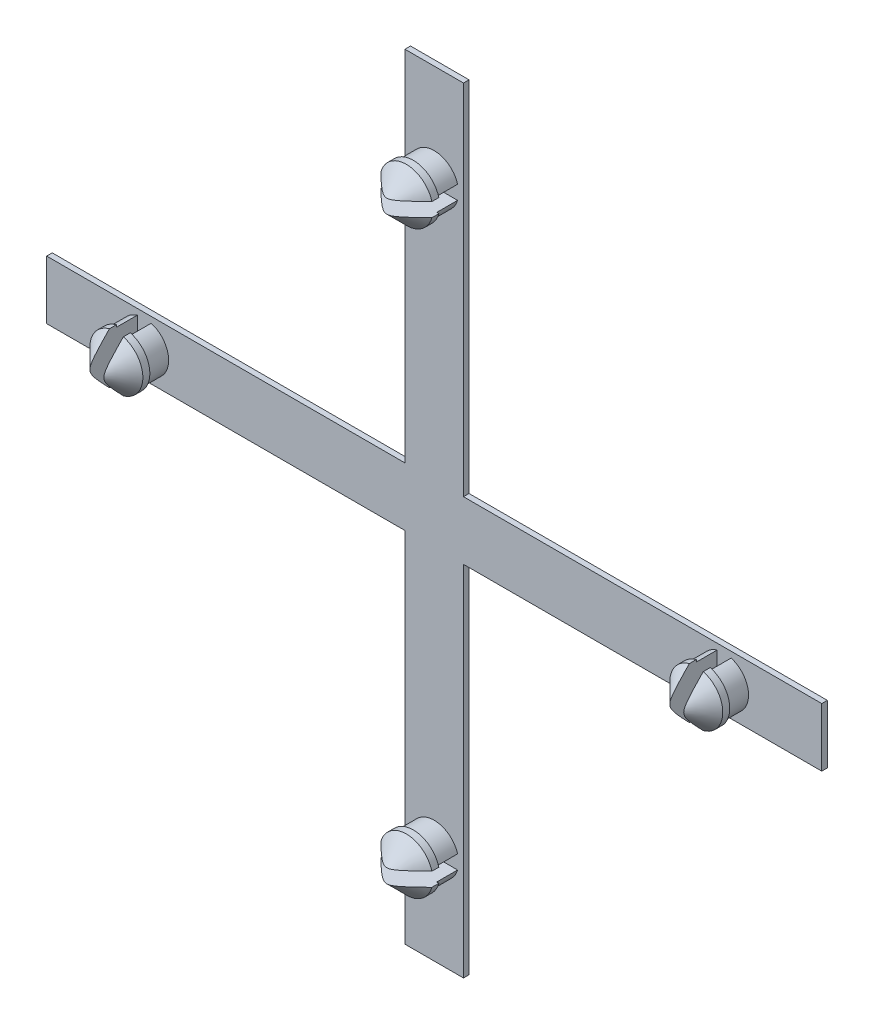
SolidWorks part; units mm, degrees
ref_plane "Přední rovina" through (0, 0, 0) normal (0, 0, 1) x (1, 0, 0)
ref_plane "Horní rovina" through (0, 0, 0) normal (0, 1, 0) x (1, 0, 0)
ref_plane "Pravá rovina" through (0, 0, 0) normal (1, 0, 0) x (0, 0, -1)
sketch "Skica2" plane through (0, 0, 0) normal (0, 0, 1) x (1, 0, 0)
  line L0 (2.1, 27.8) -> (2.1, -27.8)
  line L1 (-27.8, 2.1) -> (27.8, 2.1)
  line L2 (-27.8, 2.1) -> (-27.8, -2.1)
  line L3 (-27.8, -2.1) -> (27.8, -2.1)
  line L4 (27.8, 2.1) -> (27.8, -2.1)
  line L5 (-27.8, 2.1) -> (27.8, -2.1) construction
  line L6 (-27.8, -2.1) -> (27.8, 2.1) construction
  line L7 (2.1, 27.8) -> (-2.1, 27.8)
  line L8 (2.1, -27.8) -> (-2.1, -27.8)
  line L9 (-2.1, 27.8) -> (-2.1, -27.8)
  line L10 (27.8, -2.1) -> (-27.8, -2.1)
  line L11 (27.8, -2.1) -> (27.8, 2.1)
  line L12 (-27.8, -2.1) -> (-27.8, 2.1)
  line L13 (27.8, 2.1) -> (-27.8, 2.1)
  line L14 (-2.1, -27.8) -> (-2.1, 27.8)
  line L15 (-2.1, -27.8) -> (2.1, -27.8)
  line L16 (-2.1, 27.8) -> (2.1, 27.8)
  line L17 (2.1, -27.8) -> (2.1, 27.8)
  point P0 (0, 0)
  point P5 (0, 0)
  point P22 (0, 0)
  dimension "D1" = 4.2
  dimension "D2" = 55.6
  dimension "D3" = 4
  dimension "D7" = 0
extrude "Přidat vysunutím2" add sketch "Skica2" along normal blind 0.4 contours L9 L1 L2 L3 | L4 L1 L0 L3
sketch "Skica3" plane through (0, 0, 0.4) normal (0, 0, 1) x (1, 0, 0)
  line L0 (-27.8, 2.1) -> (-27.8, -2.1) construction
  line L1 (27.8, -2.1) -> (27.8, 2.1) construction
  line L2 (27.8, 2.1) -> (-27.8, 2.1) construction
  line L3 (-27.8, -2.1) -> (27.8, -2.1) construction
  circle A0 centre (-20.8, 0) radius 1.75
  circle A1 centre (20.8, 0) radius 1.75
  circle A2 centre (0, 20.8) radius 1.75
  circle A3 centre (0, -20.8) radius 1.75
  circle A4 centre (20.8, 0) radius 1.75
  circle A5 centre (-20.8, 0) radius 1.75
  circle A6 centre (0, -20.8) radius 1.75
  circle A7 centre (0, 20.8) radius 1.75
  point P27 (0, 0)
  dimension "D1" = 3.5
  dimension "D3" = 3.5
  dimension "D2" = 7
  dimension "D4" = 7
  dimension "D5" = 2.1
  dimension "D6" = 2.1
  dimension "D7" = 4
extrude "Přidat vysunutím3" add sketch "Skica3" along normal blind 1.5 contours A0 | A2 | A1 | A3
sketch "Skica5" plane through (0, 0, 1.9) normal (0, 0, 1) x (1, 0, 0)
  circle A0 centre (-20.8, 0) radius 1.9
  circle A1 centre (20.8, 0) radius 1.9
  circle A2 centre (0, 20.8) radius 1.9
  circle A3 centre (0, -20.8) radius 1.9
  circle A4 centre (20.8, 0) radius 1.9
  circle A5 centre (-20.8, 0) radius 1.9
  circle A6 centre (0, -20.8) radius 1.9
  circle A7 centre (0, 20.8) radius 1.9
  point P21 (0, 0)
  dimension "D1" = 3.8
  dimension "D2" = 3.8
  dimension "D3" = 4
extrude "Přidat vysunutím5" add sketch "Skica5" along normal blind 2 contours A2 | A0 | A1 | A3
chamfer "Zkosení2" distance 1.5 angle 45 4 edges at (1.9, -20.8, 3.9) (22.7, 0, 3.9) (1.9, 20.8, 3.9) (-18.9, 0, 3.9)
sketch "Skica7" plane through (0, 0, 3.9) normal (0, 0, 1) x (1, 0, 0)
  line L0 (2.5, 20.3) -> (-2.5, 20.3)
  line L1 (-20.3, 2.5) -> (-21.3, 2.5)
  line L2 (-20.3, 2.5) -> (-20.3, -2.5)
  line L3 (-20.3, -2.5) -> (-21.3, -2.5)
  line L4 (-21.3, 2.5) -> (-21.3, -2.5)
  line L5 (-20.3, 2.5) -> (-21.3, -2.5) construction
  line L6 (-20.3, -2.5) -> (-21.3, 2.5) construction
  line L7 (20.3, 2.5) -> (21.3, 2.5)
  line L8 (20.3, 2.5) -> (20.3, -2.5)
  line L9 (20.3, -2.5) -> (21.3, -2.5)
  line L10 (21.3, 2.5) -> (21.3, -2.5)
  line L11 (20.3, 2.5) -> (21.3, -2.5) construction
  line L12 (20.3, -2.5) -> (21.3, 2.5) construction
  line L13 (2.5, 20.3) -> (2.5, 21.3)
  line L14 (2.5, 21.3) -> (-2.5, 21.3)
  line L15 (-2.5, 20.3) -> (-2.5, 21.3)
  line L16 (2.5, -20.3) -> (-2.5, -20.3)
  line L17 (2.5, -20.3) -> (2.5, -21.3)
  line L18 (2.5, -21.3) -> (-2.5, -21.3)
  line L19 (-2.5, -20.3) -> (-2.5, -21.3)
  line L20 (20.3, -2.5) -> (20.3, 2.5)
  line L21 (20.3, -2.5) -> (21.3, -2.5)
  line L22 (21.3, -2.5) -> (21.3, 2.5)
  line L23 (20.3, 2.5) -> (21.3, 2.5)
  line L24 (-20.3, -2.5) -> (-20.3, 2.5)
  line L25 (-20.3, -2.5) -> (-21.3, -2.5)
  line L26 (-21.3, -2.5) -> (-21.3, 2.5)
  line L27 (-20.3, 2.5) -> (-21.3, 2.5)
  line L28 (-2.5, -20.3) -> (2.5, -20.3)
  line L29 (-2.5, -20.3) -> (-2.5, -21.3)
  line L30 (-2.5, -21.3) -> (2.5, -21.3)
  line L31 (2.5, -20.3) -> (2.5, -21.3)
  line L32 (-2.5, 20.3) -> (2.5, 20.3)
  line L33 (-2.5, 20.3) -> (-2.5, 21.3)
  line L34 (-2.5, 21.3) -> (2.5, 21.3)
  line L35 (2.5, 20.3) -> (2.5, 21.3)
  line L36 (2.5, 20.3) -> (-2.5, 20.3)
  line L37 (2.5, 20.3) -> (2.5, 21.3)
  line L38 (2.5, 21.3) -> (-2.5, 21.3)
  line L39 (-2.5, 20.3) -> (-2.5, 21.3)
  line L40 (2.5, -20.3) -> (-2.5, -20.3)
  line L41 (2.5, -20.3) -> (2.5, -21.3)
  line L42 (2.5, -21.3) -> (-2.5, -21.3)
  line L43 (-2.5, -20.3) -> (-2.5, -21.3)
  line L44 (20.3, -2.5) -> (20.3, 2.5)
  line L45 (20.3, -2.5) -> (21.3, -2.5)
  line L46 (21.3, -2.5) -> (21.3, 2.5)
  line L47 (20.3, 2.5) -> (21.3, 2.5)
  line L48 (-20.3, -2.5) -> (-20.3, 2.5)
  line L49 (-20.3, -2.5) -> (-21.3, -2.5)
  line L50 (-21.3, -2.5) -> (-21.3, 2.5)
  line L51 (-20.3, 2.5) -> (-21.3, 2.5)
  line L52 (-2.5, -20.3) -> (2.5, -20.3)
  line L53 (-2.5, -20.3) -> (-2.5, -21.3)
  line L54 (-2.5, -21.3) -> (2.5, -21.3)
  line L55 (2.5, -20.3) -> (2.5, -21.3)
  line L56 (-2.5, 20.3) -> (2.5, 20.3)
  line L57 (-2.5, 20.3) -> (-2.5, 21.3)
  line L58 (-2.5, 21.3) -> (2.5, 21.3)
  line L59 (2.5, 20.3) -> (2.5, 21.3)
  point P0 (-20.8, 0)
  point P5 (20.8, 0)
  point P39 (0, 0)
  point P63 (0, 0)
  dimension "D1" = 5
  dimension "D2" = 1
  dimension "D3" = 5
  dimension "D4" = 1
  dimension "D5" = 4
  dimension "D6" = 4
extrude "Odebrat vysunutím1" cut sketch "Skica7" against normal blind 3.5 contours L1 L4 L3 L2 | L10 L7 L8 L9 | L16 L19 L18 L17 | L14 L15 L0 L13
equation "\"1.5.000mm\"=10"
